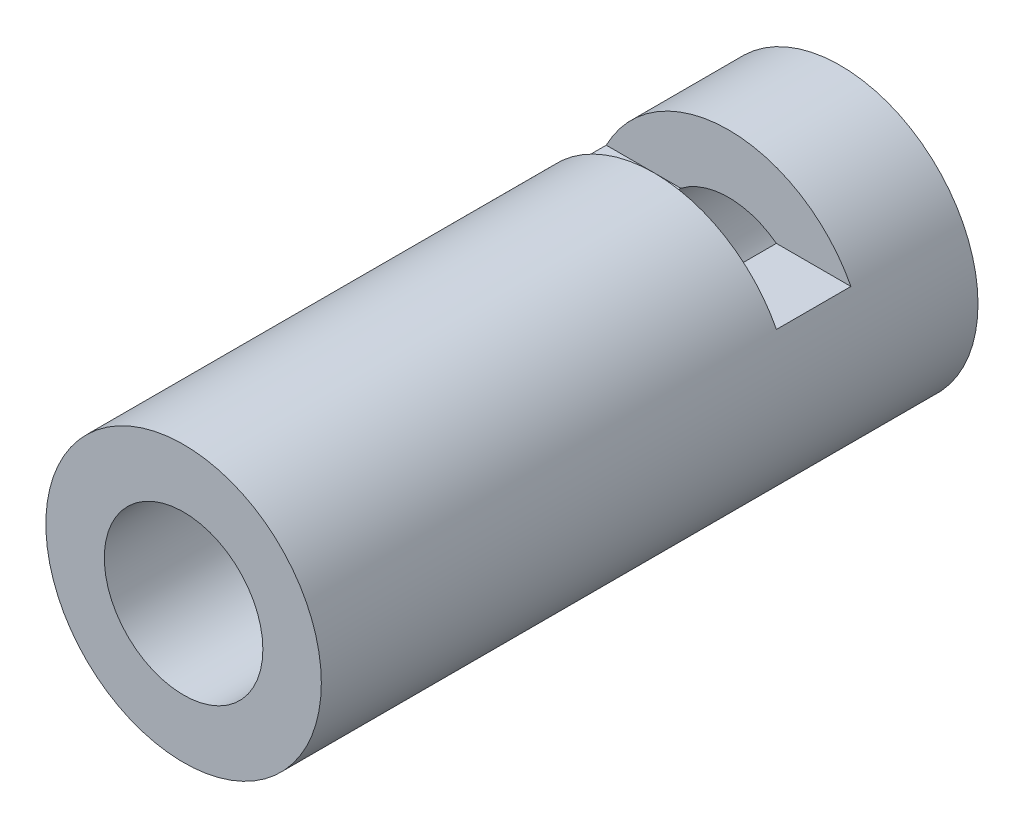
SolidWorks part; units mm, degrees
ref_plane "Ebene vorne" through (0, 0, 0) normal (0, 0, 1) x (1, 0, 0)
ref_plane "Ebene oben" through (0, 0, 0) normal (0, 1, 0) x (1, 0, 0)
ref_plane "Ebene rechts" through (0, 0, 0) normal (1, 0, 0) x (0, 0, -1)
sketch "Skizze1" plane through (0, 0, 0) normal (0, 0, 1) x (1, 0, 0)
  circle A0 centre (0, 0) radius 10.65
  circle A1 centre (0, 0) radius 18.5
  dimension "D1" = 21.3
  dimension "D2" = 37
extrude "Aufsatz-Linear austragen1" add sketch "Skizze1" along normal blind 88.2
sketch "Skizze2" plane through (0, 0, 0) normal (1, 0, 0) x (0, 0, -1)
  line L0 (0, 18.5) -> (-88.2, 18.5) construction
  line L1 (-15, 18.5) -> (-25, 18.5)
  line L2 (-15, 18.5) -> (-15, 8.5)
  line L3 (-15, 8.5) -> (-25, 8.5)
  line L4 (-25, 18.5) -> (-25, 8.5)
  line L5 (0, -18.5) -> (0, 18.5) construction
  dimension "D1" = 15
  dimension "D2" = 25
  dimension "D3" = 10
extrude "Schnitt-Linear austragen1" cut sketch "Skizze2" against normal through all and the other way through all
